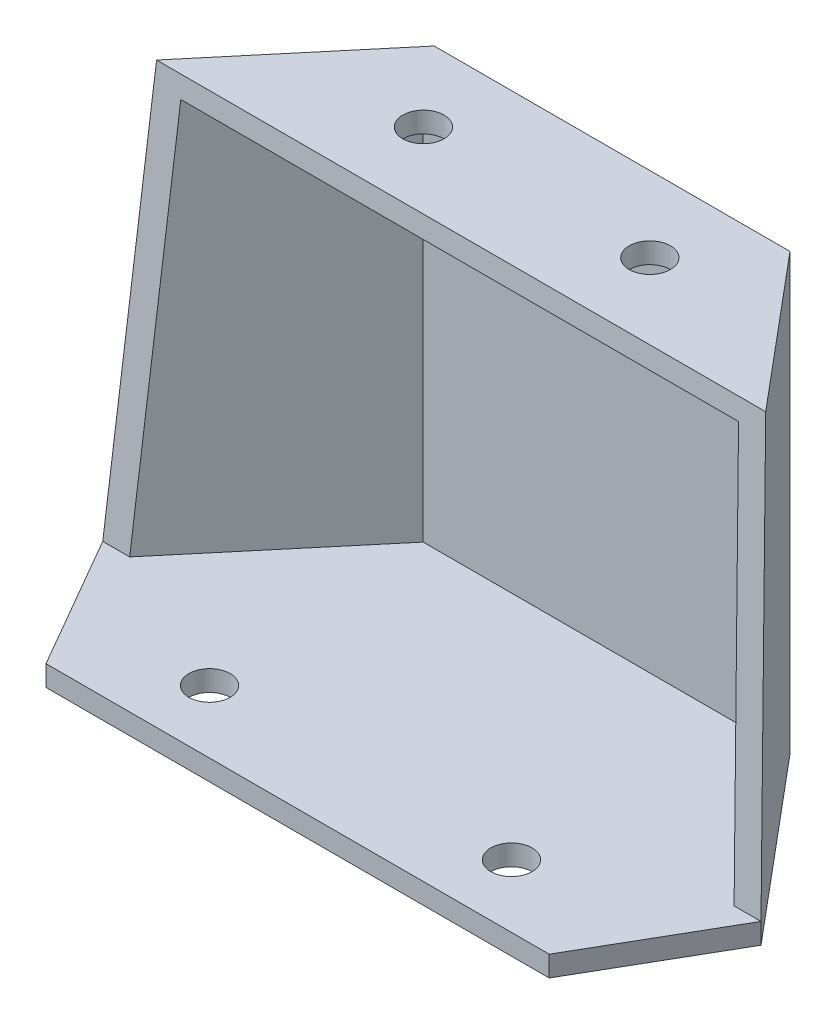
SolidWorks part; units mm, degrees
ref_plane "前视基准面" through (0, 0, 0) normal (0, 0, 1) x (1, 0, 0)
ref_plane "上视基准面" through (0, 0, 0) normal (0, 1, 0) x (1, 0, 0)
ref_plane "右视基准面" through (0, 0, 0) normal (1, 0, 0) x (0, 0, -1)
sketch "草图1" plane through (0, 0, 0) normal (0, 1, 0) x (1, 0, 0)
  line L0 (0, 0) -> (0, 152.5)
  line L1 (122, 0) -> (-122, 0)
  line L2 (-122, 0) -> (-159.5924, 65.1119)
  line L3 (-159.5924, 65.1119) -> (-86.265, 152.5)
  line L4 (-86.265, 152.5) -> (86.265, 152.5)
  line L5 (159.5924, 65.1119) -> (86.265, 152.5)
  line L6 (122, 0) -> (159.5924, 65.1119)
  dimension "D1" = 244
  dimension "D2" = 172.53
  dimension "D3" = 30
  dimension "D4" = 40
extrude "凸台-拉伸1" add sketch "草图1" along normal blind 211 contours L1 L6 L5 L4 L0 | L4 L3 L2 L1 L0
shell "抽壳2" thickness 10
sketch "草图5" plane through (0, 0, 0) normal (1, 0, 0) x (0, 0, -1)
  line L0 (79.3, 211) -> (65.1119, 10)
  line L1 (65.1119, 211) -> (152.5, 211) construction
  line L2 (65.1119, 211) -> (65.1119, 0) construction
  line L3 (0, 10) -> (65.1119, 10)
  line L4 (0, 211) -> (0, 0) construction
  line L5 (0, 211) -> (0, 10)
  line L6 (65.1119, 10) -> (152.5, 10)
  line L7 (152.5, 211) -> (152.5, 0) construction
  line L8 (152.5, 10) -> (152.5, 0)
  line L9 (79.3, 211) -> (65.1119, 12.6158)
  line L10 (79.3, 211) -> (65.1119, 10)
  line L11 (0, 10) -> (65.1119, 10)
  dimension "D1" = 10
  dimension "D2" = 73.2
extrude "切除-拉伸-薄壁2" cut sketch "草图5" against normal through all both and the other way through all thin contours L0 | L3
sketch "草图8" plane through (0, 211, 0) normal (0, 1, 0) x (1, 0, 0)
  line L0 (0, 0) -> (0, 152.5) construction
  line L1 (-86.265, 152.5) -> (86.265, 152.5) construction
  line L2 (-54.9, 115.9) -> (-54.9, 152.5)
  line L3 (-54.9, 115.9) -> (54.9, 115.9)
  circle A0 centre (-54.9, 115.9) radius 10
  circle A3 centre (54.9, 115.9) radius 10
  dimension "D2" = 20
  dimension "D3" = 36.6
  dimension "D1" = 109.8
extrude "切除-拉伸6" cut sketch "草图8" against normal blind 10 contours A3 | A0
sketch "草图13" plane through (0, 10, 0) normal (0, 1, 0) x (1, 0, 0)
  line L0 (0, 0) -> (0, 152.5) construction
  line L1 (-86.265, 152.5) -> (86.265, 152.5) construction
  line L2 (-73.2, 30.5) -> (-73.2, 0)
  line L3 (-122, 0) -> (122, 0) construction
  line L4 (-73.2, 30.5) -> (73.2, 30.5)
  circle A0 centre (-73.2, 30.5) radius 10
  circle A2 centre (73.2, 30.5) radius 10
  dimension "D1" = 20
  dimension "D2" = 30.5
  dimension "D3" = 146.4
extrude "切除-拉伸7" cut sketch "草图13" against normal blind 10 contours A0 | A2
